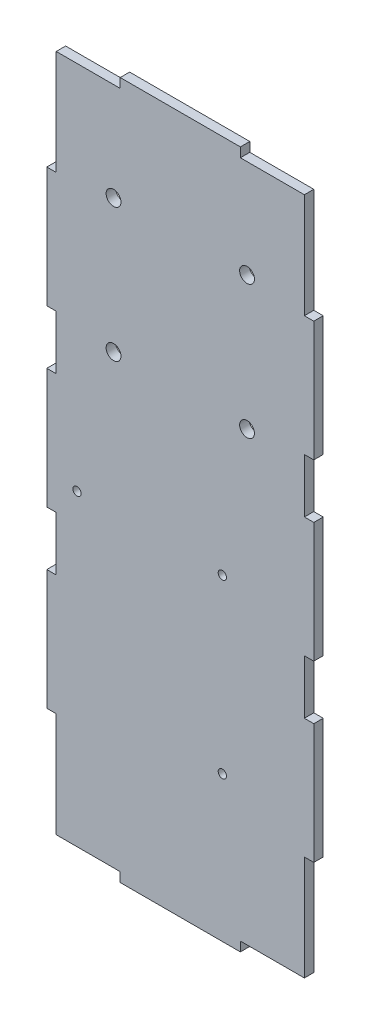
SolidWorks part; units mm, degrees
ref_plane "Front Plane" through (0, 0, 0) normal (0, 0, 1) x (1, 0, 0)
ref_plane "Top Plane" through (0, 0, 0) normal (0, 1, 0) x (1, 0, 0)
ref_plane "Right Plane" through (0, 0, 0) normal (1, 0, 0) x (0, 0, -1)
sketch "Sketch1" plane through (0, 0, 0) normal (0, 0, 1) x (1, 0, 0)
  line L0 (3.825, 57.75) -> (41.825, 57.75)
  line L1 (-39.825, -114.325) -> (-4.325, -114.325)
  line L2 (-39.825, -114.325) -> (-39.825, -99.325)
  line L3 (-39.825, -99.325) -> (-4.325, -99.325)
  line L4 (-4.325, -114.325) -> (-4.325, -99.325)
  line L5 (4.325, -114.325) -> (39.825, -114.325)
  line L6 (4.325, -114.325) -> (4.325, -99.325)
  line L7 (4.325, -99.325) -> (39.825, -99.325)
  line L8 (39.825, -114.325) -> (39.825, -99.325)
  line L9 (6.7618, 14.5) -> (23.7618, 14.5)
  line L10 (6.7618, 14.5) -> (6.7618, 40.5)
  line L11 (6.7618, 40.5) -> (23.7618, 40.5)
  line L12 (23.7618, 14.5) -> (23.7618, 40.5)
  line L13 (6.7618, 14.5) -> (23.7618, 40.5) construction
  line L14 (6.7618, 40.5) -> (23.7618, 14.5) construction
  line L15 (24.7003, 14.5) -> (41.7003, 14.5)
  line L16 (24.7003, 14.5) -> (24.7003, 40.5)
  line L17 (24.7003, 40.5) -> (41.7003, 40.5)
  line L18 (41.7003, 14.5) -> (41.7003, 40.5)
  line L19 (24.7003, 14.5) -> (41.7003, 40.5) construction
  line L20 (24.7003, 40.5) -> (41.7003, 14.5) construction
  line L21 (-10.175, -94.15) -> (40.825, -94.15)
  line L22 (-10.175, -94.15) -> (-10.175, -13.15)
  line L23 (-10.175, -13.15) -> (40.825, -13.15)
  line L24 (40.825, -94.15) -> (40.825, -13.15)
  line L25 (-10.175, -94.15) -> (40.825, -13.15) construction
  line L26 (-10.175, -13.15) -> (40.825, -94.15) construction
  line L27 (-40.825, -94.15) -> (17.675, -94.15)
  line L28 (-40.825, -94.15) -> (-40.825, -7.05)
  line L29 (-40.825, -7.05) -> (17.675, -7.05)
  line L30 (17.675, -94.15) -> (17.675, -7.05)
  line L31 (-40.825, -94.15) -> (17.675, -7.05) construction
  line L32 (-40.825, -7.05) -> (17.675, -94.15) construction
  line L33 (-41.825, 57.75) -> (-3.825, 57.75)
  line L34 (-41.825, 57.75) -> (-41.825, 107.25)
  line L35 (-41.825, 107.25) -> (-3.825, 107.25)
  line L36 (-3.825, 57.75) -> (-3.825, 107.25)
  line L37 (-41.825, 57.75) -> (-3.825, 107.25) construction
  line L38 (-41.825, 107.25) -> (-3.825, 57.75) construction
  line L39 (3.825, 57.75) -> (3.825, 107.25)
  line L40 (3.825, 107.25) -> (41.825, 107.25)
  line L41 (41.825, 57.75) -> (41.825, 107.25)
  line L42 (3.825, 57.75) -> (41.825, 107.25) construction
  line L43 (3.825, 107.25) -> (41.825, 57.75) construction
  line L44 (-45, 117.5) -> (45, -117.5) construction
  line L45 (-45, -117.5) -> (45, -117.5)
  line L46 (-45, -117.5) -> (-45, 117.5)
  line L47 (-45, 117.5) -> (45, 117.5)
  line L48 (45, -117.5) -> (45, 117.5)
  line L49 (-41.825, -117.5) -> (-41.825, 117.5) construction
  line L50 (41.825, -117.5) -> (41.825, 117.5) construction
  line L51 (-45, -114.325) -> (45, -114.325) construction
  line L52 (41.7003, 40.5) -> (6.7618, 40.5)
  line L53 (-41.825, -96.15) -> (41.825, -96.15)
  line L54 (-41.825, -96.15) -> (-41.825, -99.325)
  line L55 (-41.825, -99.325) -> (41.825, -99.325)
  line L56 (41.825, -96.15) -> (41.825, -99.325)
  line L57 (-41.825, -96.15) -> (41.825, -99.325) construction
  line L58 (-41.825, -99.325) -> (41.825, -96.15) construction
  line L59 (6.7618, 14.5) -> (41.7003, 14.5)
  line L60 (41.7003, 43.675) -> (3.5868, 43.675) construction
  line L61 (3.5868, 11.325) -> (3.5868, 43.675) construction
  line L62 (3.5868, 11.325) -> (41.7003, 11.325) construction
  circle A0 centre (14.175, -10.55) radius 1.4
  circle A1 centre (14.175, -68.55) radius 1.4
  circle A2 centre (-34.825, -10.55) radius 1.4
  circle A3 centre (37.325, -19.53) radius 1.4
  circle A4 centre (37.325, -90.65) radius 1.4
  point P8 (15.2618, 27.5)
  point P13 (33.2003, 27.5)
  point P19 (22.825, 82.5)
  point P20 (-11.575, -50.6)
  point P26 (-22.825, 82.5)
  point P28 (15.325, -53.65)
  point P59 (0, -97.7375)
  dimension "D26" = 2.8
  dimension "D29" = 71.12
  dimension "D30" = 2.8
  dimension "D1" = 15
  dimension "D2" = 35.5
  dimension "D3" = 17
  dimension "D4" = 26
  dimension "D5" = 51
  dimension "D6" = 81
  dimension "D7" = 87.1
  dimension "D8" = 58.5
  dimension "D9" = 49.5
  dimension "D10" = 38
  dimension "D11" = 90
  dimension "D12" = 235
  dimension "D15" = 1
  dimension "D16" = 2
  dimension "D18" = 2
  dimension "D19" = 2
  dimension "D20" = 3.175
  dimension "D21" = 2
  dimension "D22" = 35
  dimension "D23" = 55
  dimension "D24" = 3.5
  dimension "D25" = 3.5
  dimension "D27" = 58
  dimension "D28" = 49
  dimension "D31" = 3.5
  dimension "D32" = 3.5
  dimension "D34" = 34.9385
  dimension "D13" = 3.175
  dimension "D14" = 3.175
  dimension "D17" = 3.175
  dimension "D33" = 3.175
sketch "Sketch2" plane through (0, 0, 0) normal (1, 0, 0) x (0, 0, -1)
  line L0 (35, -114.325) -> (-35, -114.325) construction
  line L1 (35, -117.5) -> (-35, -117.5)
  line L2 (35, -117.5) -> (35, 117.5)
  line L3 (35, 117.5) -> (-35, 117.5)
  line L4 (-35, -117.5) -> (-35, 117.5)
  line L5 (35, -117.5) -> (-35, 117.5) construction
  line L6 (35, 117.5) -> (-35, -117.5) construction
  line L7 (10, 57.75) -> (-10, 57.75)
  line L8 (10, 57.75) -> (10, 107.25)
  line L9 (10, 107.25) -> (-10, 107.25)
  line L10 (-10, 57.75) -> (-10, 107.25)
  line L11 (10, 57.75) -> (-10, 107.25) construction
  line L12 (10, 107.25) -> (-10, 57.75) construction
  line L13 (25, 14.5) -> (-25, 14.5)
  line L14 (25, 14.5) -> (25, 40.5)
  line L15 (25, 40.5) -> (-25, 40.5)
  line L16 (-25, 14.5) -> (-25, 40.5)
  line L17 (25, 14.5) -> (-25, 40.5) construction
  line L18 (25, 40.5) -> (-25, 14.5) construction
  line L19 (-5.5, -114.325) -> (-25.5, -114.325)
  line L20 (-5.5, -114.325) -> (-5.5, -99.325)
  line L21 (-5.5, -99.325) -> (-25.5, -99.325)
  line L22 (-25.5, -114.325) -> (-25.5, -99.325)
  line L23 (25.475, -94.15) -> (10.475, -94.15)
  line L24 (25.475, -94.15) -> (25.475, -7.05)
  line L25 (25.475, -7.05) -> (10.475, -7.05)
  line L26 (10.475, -94.15) -> (10.475, -7.05)
  line L27 (-8.8818, -94.15) -> (-23.8818, -94.15)
  line L28 (-8.8818, -94.15) -> (-8.8818, -13.15)
  line L29 (-8.8818, -13.15) -> (-23.8818, -13.15)
  line L30 (-23.8818, -94.15) -> (-23.8818, -13.15)
  line L31 (-15.5, -99.325) -> (-15.5, -114.325) construction
  line L32 (2.325, -117.5) -> (2.325, -119.825)
  line L33 (2.325, -119.825) -> (35, -119.825)
  line L34 (-31.825, -117.5) -> (-31.825, 117.5) construction
  line L35 (-29.4447, -117.5) -> (-35, -105.5867)
  line L36 (31.825, -117.5) -> (31.825, 117.5) construction
  line L37 (35, -117.5) -> (35, -119.825)
  line L38 (-2.1092, -99.325) -> (-2.1092, -96.15)
  line L39 (-31.825, -99.325) -> (31.825, -99.325)
  line L40 (-31.825, -99.325) -> (-31.825, -96.15)
  line L41 (-31.825, -96.15) -> (31.825, -96.15)
  line L42 (31.825, -99.325) -> (31.825, -96.15)
  line L43 (-27.9557, -99.325) -> (-27.9557, -96.15)
  line L44 (0, -117.5) -> (0, 117.5) construction
  line L45 (31.825, 11.325) -> (-31.825, 11.325)
  line L46 (31.825, 11.325) -> (31.825, 14.5)
  line L47 (31.825, 14.5) -> (-31.825, 14.5)
  line L48 (-31.825, 11.325) -> (-31.825, 14.5)
  line L49 (31.825, 40.5) -> (-31.825, 40.5)
  line L50 (31.825, 40.5) -> (31.825, 43.675)
  line L51 (31.825, 43.675) -> (-31.825, 43.675)
  line L52 (-31.825, 40.5) -> (-31.825, 43.675)
  line L53 (5, -1.9843) -> (5, -96.15)
  line L54 (25.475, -96.15) -> (-25.475, -96.15)
  line L55 (25.475, -96.15) -> (25.475, -1.9843)
  line L56 (25.475, -1.9843) -> (-25.475, -1.9843)
  line L57 (-25.475, -96.15) -> (-25.475, -1.9843)
  line L58 (-5, -1.9843) -> (-5, -96.15)
  line L59 (2.325, -119.825) -> (0, -117.5)
  circle A0 centre (-15.5, -106.825) radius 13
  circle A1 centre (5, 107.25) radius 1.725
  circle A2 centre (-5, 107.25) radius 1.725
  circle A3 centre (5, 57.75) radius 1.725
  circle A4 centre (-5, 57.75) radius 1.725
  point P0 (0, 0)
  point P6 (0, 82.5)
  point P12 (0, 27.5)
  dimension "D14" = 26
  dimension "D23" = 3.45
  dimension "D1" = 235
  dimension "D2" = 70
  dimension "D3" = 20
  dimension "D4" = 49.5
  dimension "D5" = 50
  dimension "D6" = 26
  dimension "D7" = 15
  dimension "D8" = 20
  dimension "D9" = 15
  dimension "D10" = 87.1
  dimension "D11" = 15
  dimension "D12" = 81
  dimension "D16" = 19.5
  dimension "D17" = 65
  dimension "D19" = 3.175
  dimension "D20" = 6.35
  dimension "D21" = 2
  dimension "D22" = 3.175
  dimension "D24" = 10
  dimension "D25" = 5
  dimension "D26" = 6.35
  dimension "D28" = 5
  dimension "D29" = 45
  dimension "D13" = 3.175
  dimension "D15" = 3.175
  dimension "D18" = 3.175
  dimension "D27" = 10
extrude "Boss-Extrude2" add sketch "Sketch1" along normal blind 3.175 contours L45 L48 L47 L46 L59 L9 L10 L11 L52 L17 L18 L15 L30 L23 L24 L21 L27 L28 L29 L36 L33 L34 L35 L41 L0 L39 L40 L53 L56 L55 L8 L5 L6 L4 L1 L2 L54 | L33 L36 L35 L34 | L0 L41 L40 L39 | L15 L18 L17 L16 | L9 L12 L11 L10 | L12 L59 L16 L52 | L23 L30 L29 L28 L27 L22 A2 A0 | L30 L21 L24 L23 A4 A3 | L21 L30 L23 L22 A1 | L1 L4 L3 L2 | L5 L8 L7 L6 | L56 L53 L54 L55 L3 L7 | A3 | A4
sketch "Sketch4" plane through (0, 0, 3.175) normal (0, 0, 1) x (1, 0, 0)
  line L0 (0, 117.5) -> (0, 0) construction
  line L1 (-45, 117.5) -> (45, 117.5) construction
  line L2 (-45, 58.75) -> (45, 58.75) construction
  line L3 (45, -117.5) -> (45, 117.5) construction
  line L4 (-45, 0) -> (45, 0) construction
  line L5 (41.825, -79) -> (48.175, -38.5) construction
  line L6 (41.825, 38.5) -> (48.175, 38.5)
  line L7 (41.825, 38.5) -> (41.825, 79)
  line L8 (41.825, 79) -> (48.175, 79)
  line L9 (48.175, 38.5) -> (48.175, 79)
  line L10 (41.825, 38.5) -> (48.175, 79) construction
  line L11 (41.825, 79) -> (48.175, 38.5) construction
  line L12 (41.825, -20.25) -> (48.175, -20.25)
  line L13 (41.825, -20.25) -> (41.825, 20.25)
  line L14 (41.825, 20.25) -> (48.175, 20.25)
  line L15 (48.175, -20.25) -> (48.175, 20.25)
  line L16 (41.825, -20.25) -> (48.175, 20.25) construction
  line L17 (41.825, 20.25) -> (48.175, -20.25) construction
  line L18 (41.825, -38.5) -> (48.175, -79) construction
  line L19 (48.175, -38.5) -> (48.175, -79)
  line L20 (41.825, -79) -> (48.175, -79)
  line L21 (41.825, -38.5) -> (41.825, -79)
  line L22 (41.825, -38.5) -> (48.175, -38.5)
  line L23 (-41.825, -38.5) -> (-48.175, -79) construction
  line L24 (-41.825, 20.25) -> (-48.175, -20.25) construction
  line L25 (-41.825, -20.25) -> (-48.175, 20.25) construction
  line L26 (-41.825, 79) -> (-48.175, 38.5) construction
  line L27 (-41.825, 38.5) -> (-48.175, 79) construction
  line L28 (-41.825, -79) -> (-48.175, -38.5) construction
  line L29 (-41.825, -38.5) -> (-48.175, -38.5)
  line L30 (-41.825, -38.5) -> (-41.825, -79)
  line L31 (-41.825, -79) -> (-48.175, -79)
  line L32 (-48.175, -38.5) -> (-48.175, -79)
  line L33 (-48.175, -20.25) -> (-48.175, 20.25)
  line L34 (-41.825, 20.25) -> (-48.175, 20.25)
  line L35 (-41.825, -20.25) -> (-41.825, 20.25)
  line L36 (-41.825, -20.25) -> (-48.175, -20.25)
  line L37 (-48.175, 38.5) -> (-48.175, 79)
  line L38 (-41.825, 79) -> (-48.175, 79)
  line L39 (-41.825, 38.5) -> (-41.825, 79)
  line L40 (-41.825, 38.5) -> (-48.175, 38.5)
  line L41 (41.825, 114.325) -> (-41.825, 114.325)
  line L42 (-41.825, 114.325) -> (-41.825, -114.325)
  line L43 (-41.825, -114.325) -> (41.825, -114.325)
  line L44 (41.825, -114.325) -> (41.825, 114.325)
  line L45 (-45, -117.5) -> (45, -117.5)
  line L46 (45, -117.5) -> (45, 117.5)
  line L47 (45, 117.5) -> (-45, 117.5)
  line L48 (-45, 117.5) -> (-45, -117.5)
  line L49 (-45, -117.5) -> (45, -117.5)
  line L50 (45, -117.5) -> (45, 117.5)
  line L51 (45, 117.5) -> (-45, 117.5)
  line L52 (-45, 117.5) -> (-45, -117.5)
  line L54 (-20.25, 120.675) -> (20.25, 120.675)
  line L55 (-20.25, 120.675) -> (-20.25, 114.325)
  line L56 (-20.25, 114.325) -> (20.25, 114.325)
  line L57 (20.25, 120.675) -> (20.25, 114.325)
  line L58 (-20.25, 120.675) -> (20.25, 114.325) construction
  line L59 (-20.25, 114.325) -> (20.25, 120.675) construction
  line L60 (-20.25, -120.675) -> (20.25, -120.675)
  line L61 (-20.25, -120.675) -> (-20.25, -114.325)
  line L62 (-20.25, -114.325) -> (20.25, -114.325)
  line L63 (20.25, -120.675) -> (20.25, -114.325)
  line L64 (-20.25, -120.675) -> (20.25, -114.325) construction
  line L65 (-20.25, -114.325) -> (20.25, -120.675) construction
  point P36 (0, 58.75)
  point P48 (0, -117.5)
  line M13 (-45, -117.5) -> (45, -117.5)
  line M14 (45, -117.5) -> (45, 117.5)
  line M15 (45, 117.5) -> (-45, 117.5)
  line M16 (-45, 117.5) -> (-45, -117.5)
  dimension "D1" = 3.175
  dimension "D2" = 40.5
  dimension "D5" = 40.5
  dimension "D3" = 0
  dimension "D4" = 3.175
extrude "Cut-Extrude2" cut sketch "Sketch4" against normal blind 3.175 contours L55 L51 L38 L42 L41 M16 | L57 L41 L44 L8 M15 M14 | L42 L40 L34 M16 | L42 L36 L29 M16 | L61 L43 L42 L31 M13 M16 | L63 L20 L44 L43 M13 M14 | L44 L22 L12 M14 | L44 L14 L6 M14
sketch "Sketch5" plane through (0, 0, 0) normal (0, 0, -1) x (-1, 0, 0)
  line L0 (0, 0) -> (0, 117.5) construction
  line L1 (20.25, 117.5) -> (-20.25, 117.5) construction
  line L3 (-22.5, 36.25) -> (22.5, 36.25)
  line L4 (-22.5, 36.25) -> (-22.5, 81.25)
  line L5 (-22.5, 81.25) -> (22.5, 81.25)
  line L6 (22.5, 36.25) -> (22.5, 81.25)
  line L7 (-22.5, 36.25) -> (22.5, 81.25) construction
  line L8 (-22.5, 81.25) -> (22.5, 36.25) construction
  circle A0 centre (-22.5, 81.25) radius 2.5
  circle A1 centre (22.5, 81.25) radius 2.5
  circle A2 centre (22.5, 36.25) radius 2.5
  circle A3 centre (-22.5, 36.25) radius 2.5
  point P5 (0, 58.75)
  dimension "D2" = 5
  dimension "D1" = 45
extrude "Cut-Extrude3" cut sketch "Sketch5" against normal through all contours L4 A3 L3 | L3 A3 L4 | L3 A2 L6 | L6 A2 L3 | L6 A1 L5 | L5 A1 L6 | L5 A0 L4 | L4 A0 L5
